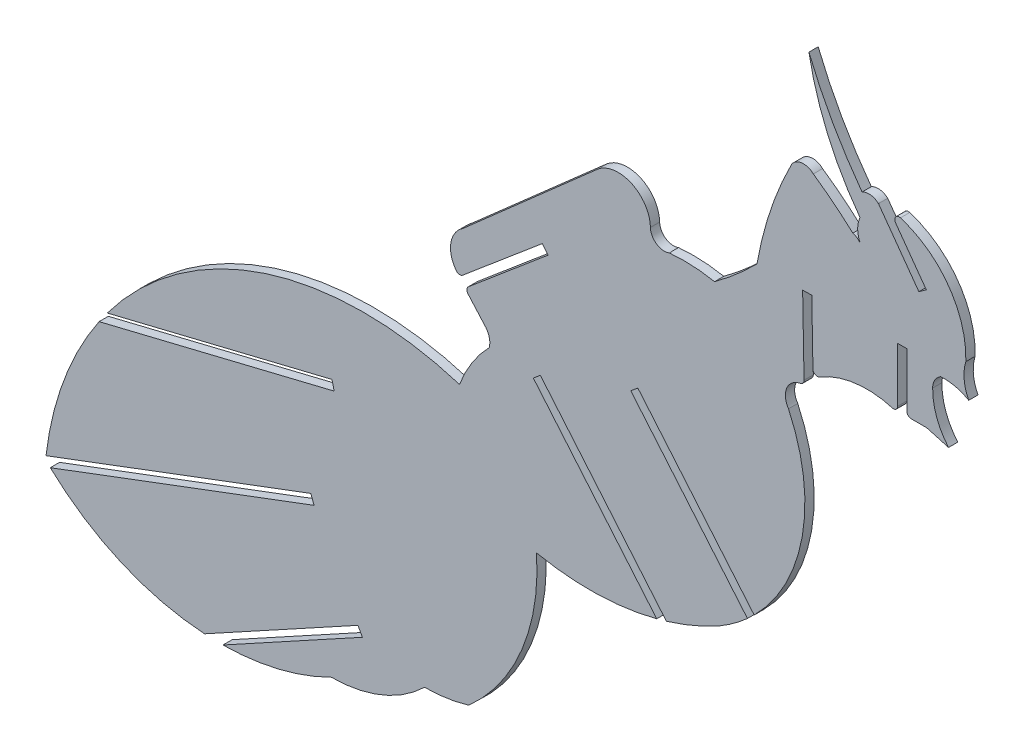
SolidWorks part; units mm, degrees
ref_plane "Front Plane" through (0, 0, 0) normal (0, 0, 1) x (1, 0, 0)
ref_plane "Top Plane" through (0, 0, 0) normal (0, 1, 0) x (1, 0, 0)
ref_plane "Right Plane" through (0, 0, 0) normal (1, 0, 0) x (0, 0, -1)
sketch "Sketch1" plane through (0, 0, 0) normal (0, 0, 1) x (1, 0, 0)
  line L0 (-18.1091, 18.6511) -> (-40.4039, -0.9924)
  line L4 (-8.4788, -40.7279) -> (-28.8091, -16.5409)
  line L5 (-28.8091, -16.5409) -> (-27.6556, -15.5715)
  line L6 (-27.6556, -15.5715) -> (-6.8883, -40.2817)
  line L12 (-39.5098, -8.8663) -> (-26.3676, 2.2205)
  line L13 (-26.3676, 2.2205) -> (-27.3389, 3.3721)
  line L14 (-27.3389, 3.3721) -> (-40.4562, -7.6939)
  line L15 (-36.909, -12.9231) -> (-39.5851, -9.8981)
  line L16 (15.7914, 5.4511) -> (15.5592, 18.1869)
  line L17 (15.5592, 18.1869) -> (17.0656, 18.2144)
  line L18 (17.0656, 18.2144) -> (17.2557, 7.7903)
  line L19 (31.2207, 9.4468) -> (31.2278, 18.4217)
  line L20 (31.2278, 18.4217) -> (32.7342, 18.4207)
  line L21 (32.7342, 18.4207) -> (32.7271, 9.4927)
  line L22 (28.0482, 36.7796) -> (34.7101, 27.5411)
  line L23 (34.7101, 27.5411) -> (35.9316, 28.4223)
  line L24 (35.9316, 28.4223) -> (30.8703, 35.4415)
  line L25 (36.001, 8.7691) -> (33.4502, 8.7691)
  line L26 (36.001, 8.7691) -> (39.5936, 7.7507)
  arc A0 (-9.522, 14.5863) -> (-18.1091, 18.6511) centre (-14.8243, 14.4877) ccw
  arc A1 (-9.522, 14.5863) -> (-6.4194, 12.505) centre (-7.24, 14.6348) ccw
  arc A2 (1.0524, 12.1435) -> (-6.4194, 12.505) centre (-3.9179, -13.1897) ccw
  arc A3 (1.0524, 12.1435) -> (8.0421, 18.1691) centre (-33.4337, 59.2141) ccw
  arc A4 (23.8292, 30.4613) -> (17.3216, 35.6434) centre (-17.4727, -14.7286) ccw
  arc A5 (17.3216, 35.6434) -> (13.768, 35.2781) centre (15.7028, 33.9236) ccw
  arc A6 (25.0145, 33.2747) -> (25.0144, 29.677) centre (29.0382, 31.4758) ccw
  arc A7 (28.0482, 36.7796) -> (25.3516, 37.0858) centre (26.4877, 35.0649) ccw
  arc A8 (39.5936, 7.7507) -> (36.981, 14.9313) centre (47.8288, 14.8126) cw
  arc A9 (42.4479, 21.4263) -> (31.6703, 36.5553) centre (27.1512, 21.9326) ccw
  arc A10 (38.2908, 17.205) -> (36.981, 14.9313) centre (39.5936, 14.9404) ccw
  arc A11 (25.0145, 33.2747) -> (16.594, 52.6637) centre (61.9939, 60.8574) cw
  arc A12 (15.1644, 4.6873) -> (13.2242, 0.0922) centre (15.6913, 1.7577) ccw
  arc A13 (1.8961, -36.5434) -> (13.2242, 0.0922) centre (-12.4855, -12.0273) ccw
  arc A14 (-36.0655, -15.8155) -> (-40.9707, -23.5336) centre (-20.1889, -31.3236) ccw
  arc A15 (-36.0655, -15.8155) -> (-36.909, -12.9231) centre (-38.9665, -15.0924) ccw
  arc A16 (1.8961, -36.5434) -> (-6.8883, -40.2817) centre (-19.4422, 1.4089) cw
  arc A18 (-40.4039, -0.9924) -> (-41.4919, -7.5868) centre (-37.9173, -4.7896) ccw
  arc A19 (-8.4788, -40.7279) -> (-28.2873, -41.2229) centre (-19.4422, 1.4089) cw
  arc A20 (-28.2873, -41.2229) -> (-39.4402, -68.5396) centre (-61.5122, -43.5928) cw
  arc A21 (-39.4402, -68.5396) -> (-46.7323, -69.6276) centre (-46.7323, -44.6475) cw
  arc A22 (-46.7323, -69.6276) -> (-62.0754, -75.8687) centre (-62.0754, -53.8886) cw
  arc A23 (-62.0754, -75.8687) -> (-109.1644, -68.3746) centre (-80.3971, -39.3039) cw
  arc A24 (17.2557, 7.7903) -> (18.3907, 7.2093) centre (17.9786, 7.8034) ccw
  arc A25 (30.4976, 8.7243) -> (31.2207, 9.4468) centre (30.4976, 9.4473) ccw
  arc A26 (32.7271, 9.4927) -> (33.4502, 8.7691) centre (33.4502, 9.4922) ccw
  arc A27 (30.4976, 8.7243) -> (18.3907, 7.2093) centre (26.1567, -5.7189) ccw
  arc A28 (31.6703, 36.5553) -> (30.8703, 35.4415) centre (31.4568, 35.8644) ccw
  arc A29 (13.768, 35.2781) -> (8.0421, 18.1691) centre (67.1808, 7.8898) ccw
  arc A30 (-39.5098, -8.8663) -> (-39.5851, -9.8981) centre (-39.0435, -9.419) ccw
  arc A31 (-41.4919, -7.5868) -> (-40.4562, -7.6939) centre (-40.9224, -7.1412) ccw
  arc A32 (15.1644, 4.6873) -> (15.7914, 5.4511) centre (15.0295, 5.4372) ccw
  arc A33 (42.4479, 21.4263) -> (42.9261, 16.1474) centre (49.1229, 19.37) ccw
  arc A34 (42.9261, 16.1474) -> (38.2908, 17.205) centre (38.916, 9.2579) ccw
  arc A35 (16.594, 52.6637) -> (25.3516, 37.0858) centre (82.4574, 79.4402) ccw
  arc A36 (25.0144, 29.677) -> (23.8292, 30.4613) centre (23.1583, 28.1599) ccw
  arc A37 (-109.1644, -68.3746) -> (-40.9707, -23.5336) centre (-56.7056, -73.8788) cw
  dimension "D1" = 0.762
extrude "Boss-Extrude1" add sketch "Sketch1" along normal blind 1.524
sketch "Sketch2" plane through (0, 0, 0) normal (0, 0, -1) x (-1, 0, 0)
  line L0 (-7.4123, -34.3339) -> (12.7565, -10.3359)
  line L1 (12.7565, -10.3359) -> (11.5898, -9.3554)
  line L2 (11.5898, -9.3554) -> (-8.579, -33.3534)
  line L3 (-8.579, -33.3534) -> (-7.4123, -34.3339)
extrude "Cut-Extrude1" cut sketch "Sketch2" against normal blind 1.524
sketch "Sketch3" plane through (0, 0, 0) normal (0, 0, -1) x (-1, 0, 0)
  line L1 (92.2394, -85.1954) -> (57.6987, -66.2699)
  line L2 (91.5071, -86.5319) -> (56.9664, -67.6064)
  line L3 (92.2394, -85.1954) -> (91.5071, -86.5319)
  line L4 (57.6987, -66.2699) -> (56.9664, -67.6064)
  line L6 (113.5689, -69.4436) -> (65.4683, -51.3346)
  line L7 (113.032, -70.8699) -> (64.9313, -52.7608)
  line L8 (113.5689, -69.4436) -> (113.032, -70.8699)
  line L9 (65.4683, -51.3346) -> (64.9313, -52.7608)
  line L11 (103.8925, -43.5566) -> (61.9819, -33.3296)
  line L12 (103.5313, -45.0372) -> (61.6207, -34.8101)
  line L13 (103.8925, -43.5566) -> (103.5313, -45.0372)
  line L14 (61.9819, -33.3296) -> (61.6207, -34.8101)
extrude "Cut-Extrude2" cut sketch "Sketch3" against normal blind 1.524
